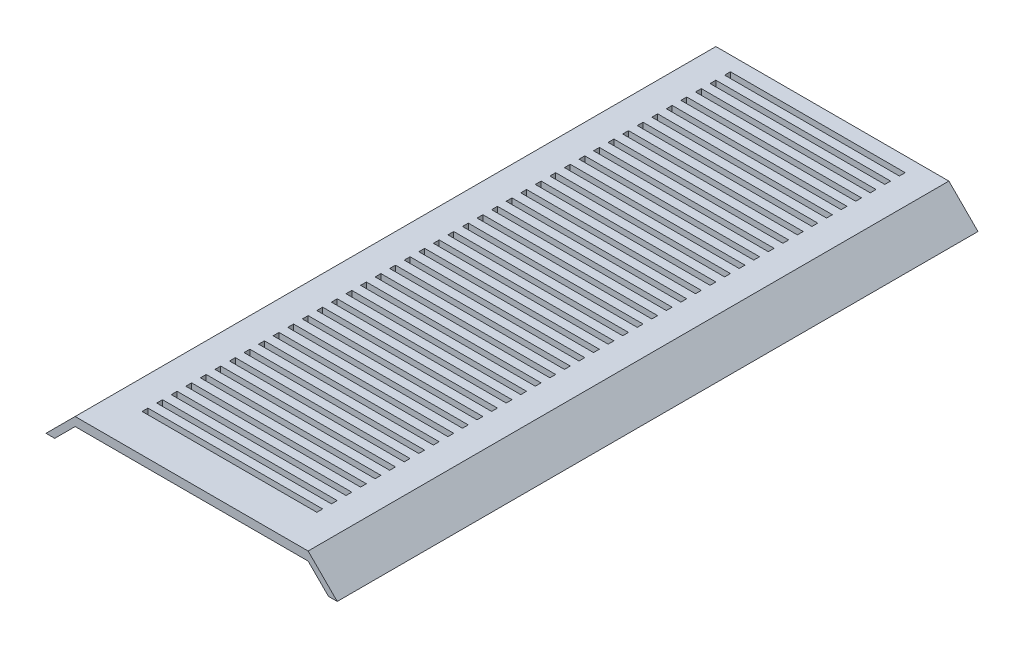
SolidWorks part; units mm, degrees
ref_plane "Alzado" through (0, 0, 0) normal (0, 0, 1) x (1, 0, 0)
ref_plane "Planta" through (0, 0, 0) normal (0, 1, 0) x (1, 0, 0)
ref_plane "Vista lateral" through (0, 0, 0) normal (1, 0, 0) x (0, 0, -1)
sketch "Croquis1" plane through (0, 0, 0) normal (0, 0, 1) x (1, 0, 0)
  line L0 (-47, 0) -> (47, 0) construction
  line L1 (-47, 0) -> (-50, 0)
  line L2 (47, 0) -> (50, 0)
  line L3 (-47, 0) -> (-40, 7)
  line L4 (-40, 7) -> (40, 7)
  line L5 (40, 7) -> (47, 0)
  line L6 (-50, 0) -> (-40, 10)
  line L7 (-40, 10) -> (40, 10)
  line L8 (40, 10) -> (50, 0)
  point P4 (0, 0)
  dimension "D1" = 94
  dimension "D2" = 3
  dimension "D3" = 135
  dimension "D4" = 135
  dimension "D5" = 7
  dimension "D6" = 3
extrude "Saliente-Extruir1" add sketch "Croquis1" along normal blind 220
sketch "Croquis2" plane through (0, 10, 0) normal (0, 1, 0) x (1, 0, 0)
  line L0 (0, -5) -> (0, 0) construction
  line L1 (-30, -7) -> (30, -7)
  line L2 (-30, -7) -> (-30, -5)
  line L3 (-30, -5) -> (30, -5)
  line L4 (30, -7) -> (30, -5)
  line L5 (-30, -7) -> (30, -5) construction
  line L6 (-30, -5) -> (30, -7) construction
  line L7 (40, 0) -> (-40, 0) construction
  line L8 (-30, -12) -> (-30, -10)
  line L9 (-30, -10) -> (30, -10)
  line L10 (-30, -12) -> (30, -12)
  line L11 (30, -12) -> (30, -10)
  line L12 (-30, -17) -> (-30, -15)
  line L13 (-30, -15) -> (30, -15)
  line L14 (-30, -17) -> (30, -17)
  line L15 (30, -17) -> (30, -15)
  line L16 (-30, -22) -> (-30, -20)
  line L17 (-30, -20) -> (30, -20)
  line L18 (-30, -22) -> (30, -22)
  line L19 (30, -22) -> (30, -20)
  line L20 (-30, -27) -> (-30, -25)
  line L21 (-30, -25) -> (30, -25)
  line L22 (-30, -27) -> (30, -27)
  line L23 (30, -27) -> (30, -25)
  line L24 (-30, -32) -> (-30, -30)
  line L25 (-30, -30) -> (30, -30)
  line L26 (-30, -32) -> (30, -32)
  line L27 (30, -32) -> (30, -30)
  line L28 (-30, -37) -> (-30, -35)
  line L29 (-30, -35) -> (30, -35)
  line L30 (-30, -37) -> (30, -37)
  line L31 (30, -37) -> (30, -35)
  line L32 (-30, -42) -> (-30, -40)
  line L33 (-30, -40) -> (30, -40)
  line L34 (-30, -42) -> (30, -42)
  line L35 (30, -42) -> (30, -40)
  line L36 (-30, -47) -> (-30, -45)
  line L37 (-30, -45) -> (30, -45)
  line L38 (-30, -47) -> (30, -47)
  line L39 (30, -47) -> (30, -45)
  line L40 (-30, -52) -> (-30, -50)
  line L41 (-30, -50) -> (30, -50)
  line L42 (-30, -52) -> (30, -52)
  line L43 (30, -52) -> (30, -50)
  line L44 (-30, -57) -> (-30, -55)
  line L45 (-30, -55) -> (30, -55)
  line L46 (-30, -57) -> (30, -57)
  line L47 (30, -57) -> (30, -55)
  line L48 (-30, -62) -> (-30, -60)
  line L49 (-30, -60) -> (30, -60)
  line L50 (-30, -62) -> (30, -62)
  line L51 (30, -62) -> (30, -60)
  line L52 (-30, -67) -> (-30, -65)
  line L53 (-30, -65) -> (30, -65)
  line L54 (-30, -67) -> (30, -67)
  line L55 (30, -67) -> (30, -65)
  line L56 (-30, -72) -> (-30, -70)
  line L57 (-30, -70) -> (30, -70)
  line L58 (-30, -72) -> (30, -72)
  line L59 (30, -72) -> (30, -70)
  line L60 (-30, -77) -> (-30, -75)
  line L61 (-30, -75) -> (30, -75)
  line L62 (-30, -77) -> (30, -77)
  line L63 (30, -77) -> (30, -75)
  line L64 (-30, -82) -> (-30, -80)
  line L65 (-30, -80) -> (30, -80)
  line L66 (-30, -82) -> (30, -82)
  line L67 (30, -82) -> (30, -80)
  line L68 (-30, -87) -> (-30, -85)
  line L69 (-30, -85) -> (30, -85)
  line L70 (-30, -87) -> (30, -87)
  line L71 (30, -87) -> (30, -85)
  line L72 (-30, -92) -> (-30, -90)
  line L73 (-30, -90) -> (30, -90)
  line L74 (-30, -92) -> (30, -92)
  line L75 (30, -92) -> (30, -90)
  line L76 (-30, -97) -> (-30, -95)
  line L77 (-30, -95) -> (30, -95)
  line L78 (-30, -97) -> (30, -97)
  line L79 (30, -97) -> (30, -95)
  line L80 (-30, -102) -> (-30, -100)
  line L81 (-30, -100) -> (30, -100)
  line L82 (-30, -102) -> (30, -102)
  line L83 (30, -102) -> (30, -100)
  line L84 (-30, -107) -> (-30, -105)
  line L85 (-30, -105) -> (30, -105)
  line L86 (-30, -107) -> (30, -107)
  line L87 (30, -107) -> (30, -105)
  line L88 (-30, -112) -> (-30, -110)
  line L89 (-30, -110) -> (30, -110)
  line L90 (-30, -112) -> (30, -112)
  line L91 (30, -112) -> (30, -110)
  line L92 (-30, -117) -> (-30, -115)
  line L93 (-30, -115) -> (30, -115)
  line L94 (-30, -117) -> (30, -117)
  line L95 (30, -117) -> (30, -115)
  line L96 (-30, -122) -> (-30, -120)
  line L97 (-30, -120) -> (30, -120)
  line L98 (-30, -122) -> (30, -122)
  line L99 (30, -122) -> (30, -120)
  line L100 (-30, -127) -> (-30, -125)
  line L101 (-30, -125) -> (30, -125)
  line L102 (-30, -127) -> (30, -127)
  line L103 (30, -127) -> (30, -125)
  line L104 (-30, -132) -> (-30, -130)
  line L105 (-30, -130) -> (30, -130)
  line L106 (-30, -132) -> (30, -132)
  line L107 (30, -132) -> (30, -130)
  line L108 (-30, -137) -> (-30, -135)
  line L109 (-30, -135) -> (30, -135)
  line L110 (-30, -137) -> (30, -137)
  line L111 (30, -137) -> (30, -135)
  line L112 (-30, -142) -> (-30, -140)
  line L113 (-30, -140) -> (30, -140)
  line L114 (-30, -142) -> (30, -142)
  line L115 (30, -142) -> (30, -140)
  line L116 (-30, -147) -> (-30, -145)
  line L117 (-30, -145) -> (30, -145)
  line L118 (-30, -147) -> (30, -147)
  line L119 (30, -147) -> (30, -145)
  line L120 (-30, -152) -> (-30, -150)
  line L121 (-30, -150) -> (30, -150)
  line L122 (-30, -152) -> (30, -152)
  line L123 (30, -152) -> (30, -150)
  line L124 (-30, -157) -> (-30, -155)
  line L125 (-30, -155) -> (30, -155)
  line L126 (-30, -157) -> (30, -157)
  line L127 (30, -157) -> (30, -155)
  line L128 (-30, -162) -> (-30, -160)
  line L129 (-30, -160) -> (30, -160)
  line L130 (-30, -162) -> (30, -162)
  line L131 (30, -162) -> (30, -160)
  line L132 (-30, -167) -> (-30, -165)
  line L133 (-30, -165) -> (30, -165)
  line L134 (-30, -167) -> (30, -167)
  line L135 (30, -167) -> (30, -165)
  line L136 (-30, -172) -> (-30, -170)
  line L137 (-30, -170) -> (30, -170)
  line L138 (-30, -172) -> (30, -172)
  line L139 (30, -172) -> (30, -170)
  line L140 (-30, -177) -> (-30, -175)
  line L141 (-30, -175) -> (30, -175)
  line L142 (-30, -177) -> (30, -177)
  line L143 (30, -177) -> (30, -175)
  line L144 (-30, -182) -> (-30, -180)
  line L145 (-30, -180) -> (30, -180)
  line L146 (-30, -182) -> (30, -182)
  line L147 (30, -182) -> (30, -180)
  line L148 (-30, -187) -> (-30, -185)
  line L149 (-30, -185) -> (30, -185)
  line L150 (-30, -187) -> (30, -187)
  line L151 (30, -187) -> (30, -185)
  line L152 (-30, -192) -> (-30, -190)
  line L153 (-30, -190) -> (30, -190)
  line L154 (-30, -192) -> (30, -192)
  line L155 (30, -192) -> (30, -190)
  line L156 (-30, -197) -> (-30, -195)
  line L157 (-30, -195) -> (30, -195)
  line L158 (-30, -197) -> (30, -197)
  line L159 (30, -197) -> (30, -195)
  line L160 (-30, -202) -> (-30, -200)
  line L161 (-30, -200) -> (30, -200)
  line L162 (-30, -202) -> (30, -202)
  line L163 (30, -202) -> (30, -200)
  line L164 (-30, -207) -> (-30, -205)
  line L165 (-30, -205) -> (30, -205)
  line L166 (-30, -207) -> (30, -207)
  line L167 (30, -207) -> (30, -205)
  line L172 (-30, -210) -> (30, -210) [skipped]
  line L173 (-30, -212) -> (30, -212) [skipped]
  line L174 (-30, -212) -> (-30, -210) [skipped]
  line L175 (30, -212) -> (30, -210) [skipped]
  point P0 (0, -6)
  dimension "D1" = 2
  dimension "D2" = 60
  dimension "D3" = 5
  dimension "D4" = 42
extrude "Cortar-Extruir1" cut sketch "Croquis2" against normal blind 10
